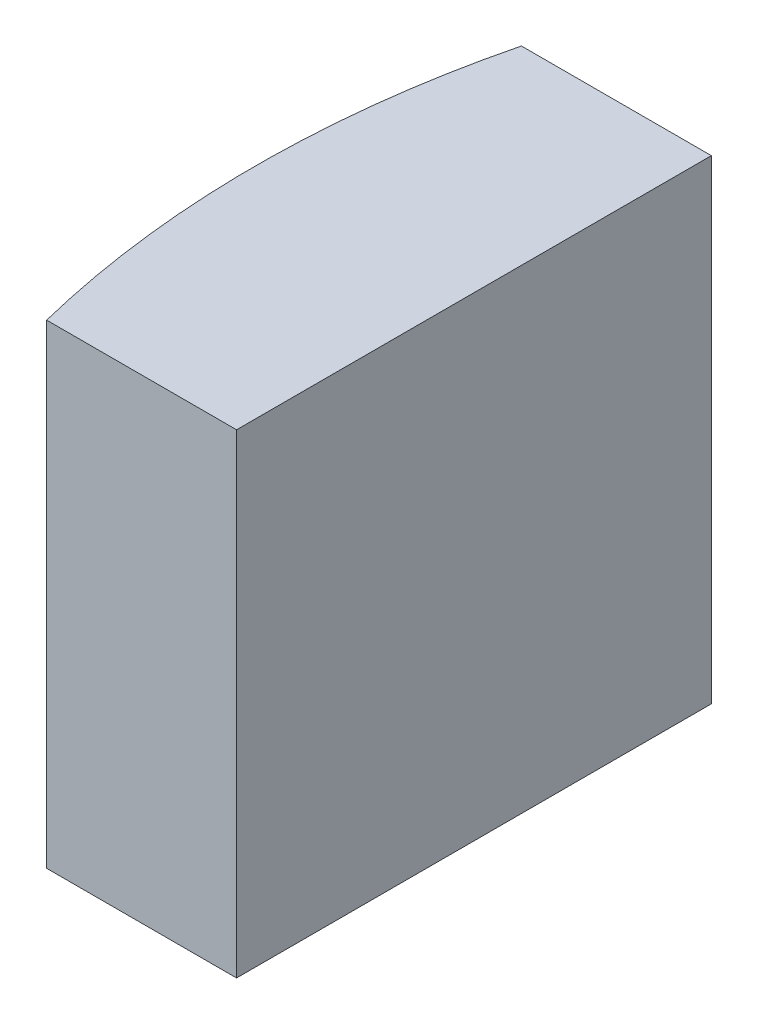
SolidWorks part; units mm, degrees
ref_plane "前视基准面" through (0, 0, 0) normal (0, 0, 1) x (1, 0, 0)
ref_plane "上视基准面" through (0, 0, 0) normal (0, 1, 0) x (1, 0, 0)
ref_plane "右视基准面" through (0, 0, 0) normal (1, 0, 0) x (0, 0, -1)
sketch "草图1" plane through (0, 0, 0) normal (0, 1, 0) x (1, 0, 0)
  line L0 (0, 0) -> (0, -5)
  line L1 (0, 0) -> (-2, 0)
  line L2 (0, -5) -> (-2, -5)
  line L3 (0, -2.5) -> (6.7931, -2.5) construction
  arc A0 (-2, 0) -> (-2, -5) centre (8.0229, -2.5) ccw
  dimension "D2" = 10.33
  dimension "D3" = 2
  dimension "D1" = 5
extrude "凸台-拉伸1" add sketch "草图1" along normal blind 5
